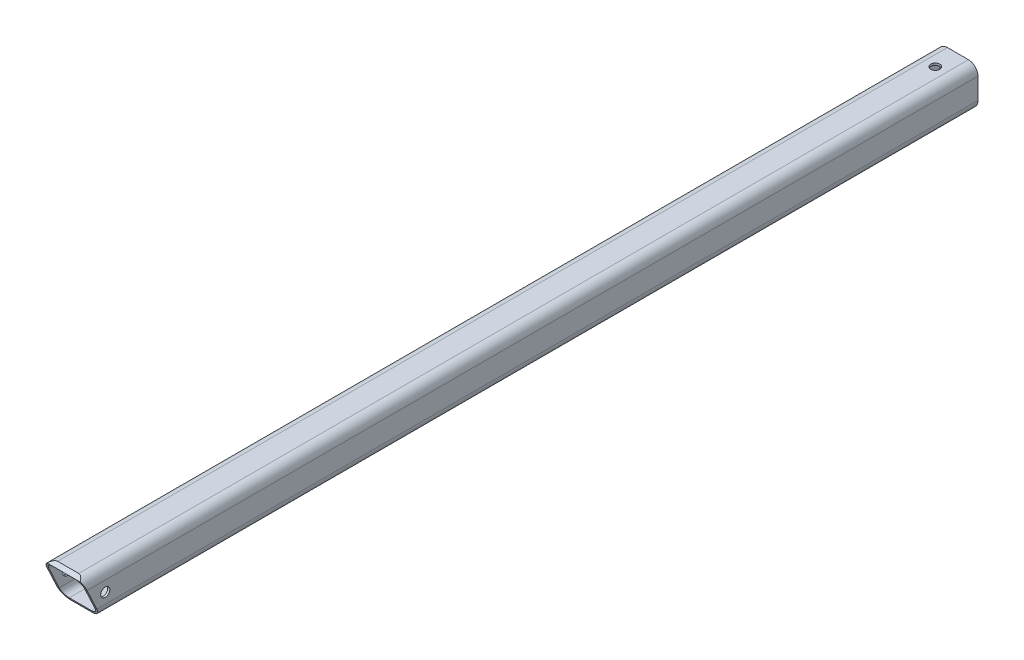
SolidWorks part; units mm, degrees
material "Carbon Fiber"
ref_plane "Front Plane" through (0, 0, 0) normal (0, 0, 1) x (1, 0, 0)
ref_plane "Top Plane" through (0, 0, 0) normal (0, 1, 0) x (1, 0, 0)
ref_plane "Right Plane" through (0, 0, 0) normal (1, 0, 0) x (0, 0, -1)
sketch "Sketch4" plane through (0, 0, 0) normal (0, 0, 1) x (1, 0, 0)
  line L1 (11.2268, -11.2268) -> (-11.2268, -11.2268)
  line L2 (11.2268, -11.2268) -> (11.2268, 11.2268)
  line L3 (11.2268, 11.2268) -> (-11.2268, 11.2268)
  line L4 (-11.2268, -11.2268) -> (-11.2268, 11.2268)
  line L5 (11.2268, -11.2268) -> (-11.2268, 11.2268) construction
  line L6 (11.2268, 11.2268) -> (-11.2268, -11.2268) construction
  line L7 (10.033, -10.033) -> (-10.033, -10.033)
  line L8 (10.033, -10.033) -> (10.033, 10.033)
  line L9 (10.033, 10.033) -> (-10.033, 10.033)
  line L10 (-10.033, -10.033) -> (-10.033, 10.033)
  line L11 (10.033, -10.033) -> (-10.033, 10.033) construction
  line L12 (10.033, 10.033) -> (-10.033, -10.033) construction
  point P0 (0, 0)
  point P1 (0, 0)
  dimension "D1" = 20.066
  dimension "D2" = 22.4536
extrude "Boss-Extrude2" add sketch "Sketch4" along normal blind 501.65
fillet "Fillet2" radius 3.81 4 edges at (-10.033, -10.033, 250.825) (10.033, -10.033, 250.825) (10.033, 10.033, 250.825) (-10.033, 10.033, 250.825)
fillet "Fillet1" radius 5.334 4 edges at (-11.2268, -11.2268, 250.825) (11.2268, -11.2268, 250.825) (-11.2268, 11.2268, 250.825) (11.2268, 11.2268, 250.825)
hole_wizard "#10 Clearance Hole1" positions "Sketch6" profile "Sketch7" hole size "#10" standard "ANSI Inch"
sketch "Sketch6" plane through (0, 11.2268, 0) normal (0, 1, 0) x (1, 0, 0)
  line L0 (5.8928, 0) -> (-5.8928, 0) construction
  point P0 (0, -12.7)
  point P6 (0, 0)
  dimension "D1" = 12.7
sketch "Sketch7" plane through (0, 11.2268, 12.7) normal (1, 0, 0) x (0, 0, 1)
  line L0 (0, 0) -> (0, 18.0438)
  line L1 (0, 18.0438) -> (2.5527, 16.51)
  line L2 (2.5527, 16.51) -> (2.5527, 0)
  line L5 (2.5527, 0) -> (0, 0)
  line L10 (0, 18.0438) -> (-2.5527, 16.51) construction
  line L11 (0, -6.35) -> (0, 107.95) construction
  dimension "Hole Dia." = 5.1054
  dimension "Hole Depth" = 16.51
  dimension "Drill Angle" = 118
hole_wizard "#10 Clearance Hole2" positions "Sketch8" profile "Sketch9" hole size "#10" standard "ANSI Inch" end condition through all
sketch "Sketch8" plane through (11.2268, 0, 0) normal (1, 0, 0) x (0, 0, -1)
  line L0 (-501.65, -5.8928) -> (-501.65, 5.8928) construction
  line L1 (0, 11.2268) -> (-501.65, 11.2268) construction
  point P0 (-488.95, 0)
  dimension "D1" = 12.7
  dimension "D2" = 11.2268
sketch "Sketch9" plane through (11.2268, 0, 488.95) normal (0, 1, 0) x (0, 0, -1)
  line L0 (0, 0) -> (0, 22.4536)
  line L1 (0, 22.4536) -> (2.5527, 22.4536)
  line L2 (2.5527, 22.4536) -> (2.5527, 0)
  line L5 (2.5527, 0) -> (0, 0)
  line L11 (0, -6.35) -> (0, 107.95) construction
  dimension "Thru Hole Dia." = 5.1054
  dimension "Thru Hole Depth" = 22.4536
sketch "Sketch10" plane through (-11.2268, 0, 0) normal (-1, 0, 0) x (0, 0, 1)
  line L0 (501.65, 11.2268) -> (491.1797, -11.2268)
  line L1 (501.65, -11.2268) -> (0, -11.2268) construction
  line L2 (491.1797, -11.2268) -> (501.65, -11.2268)
  line L3 (501.65, -11.2268) -> (501.65, 11.2268)
  dimension "D1" = 25
extrude "Cut-Extrude1" cut sketch "Sketch10" against normal through all contours L0 L2 L3
sketch "Sketch11" plane through (-11.2268, 0, 0) normal (-1, 0, 0) x (0, 0, 1)
  line L0 (501.65, 11.2268) -> (0, 11.2268) construction
  line L1 (0, 10.033) -> (501.0933, 10.033) construction
  line L2 (501.65, 11.2268) -> (498.5332, 11.2268)
  line L3 (0, 10.033) -> (501.0933, 10.033) construction
  line L4 (501.65, 11.2268) -> (501.0933, 10.033)
  line L5 (501.0933, 10.033) -> (498.5332, 11.2268)
extrude "Cut-Extrude2" cut sketch "Sketch11" against normal through all
